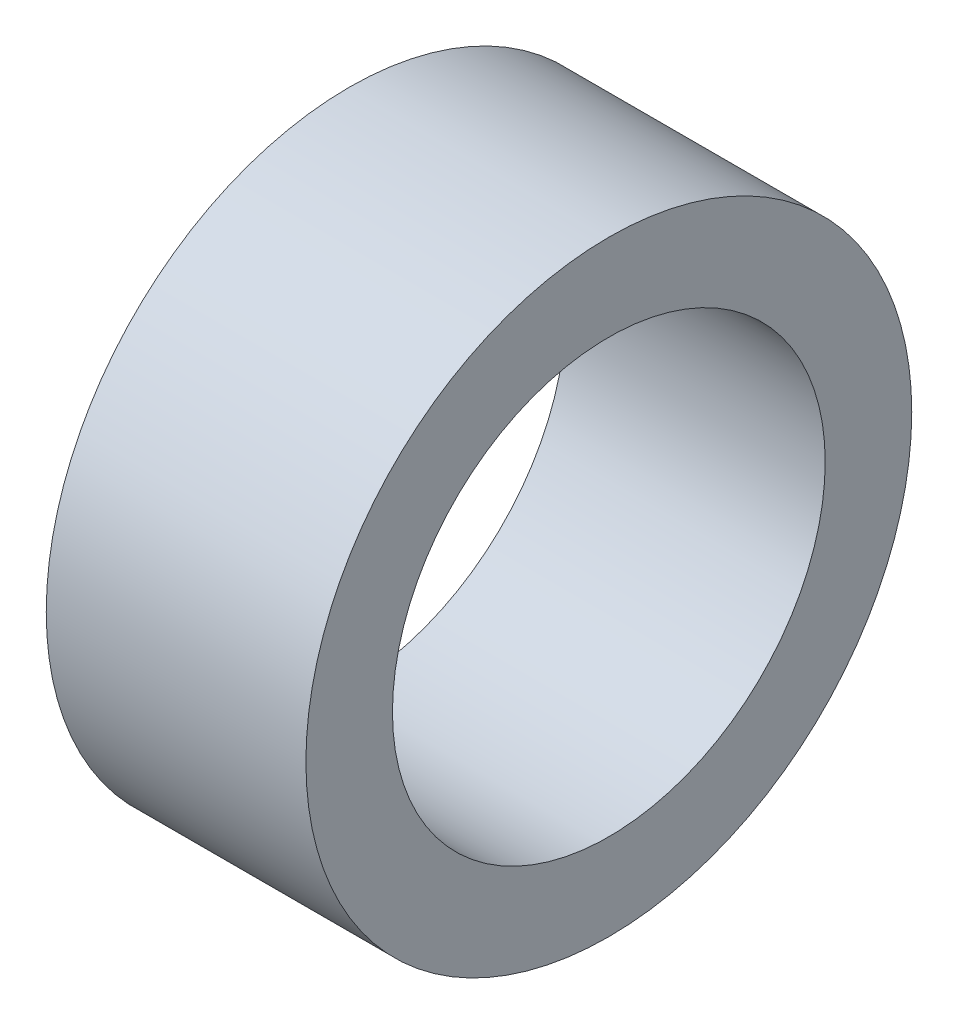
SolidWorks part; units mm, degrees
ref_plane "前视基准面" through (0, 0, 0) normal (0, 0, 1) x (1, 0, 0)
ref_plane "上视基准面" through (0, 0, 0) normal (0, 1, 0) x (1, 0, 0)
ref_plane "右视基准面" through (0, 0, 0) normal (1, 0, 0) x (0, 0, -1)
sketch "草图1" plane through (0, 0, 0) normal (1, 0, 0) x (0, 0, -1)
  circle A0 centre (0, 0) radius 7
  circle A1 centre (0, 0) radius 5
  dimension "D1" = 10
  dimension "D2" = 14
extrude "凸台-拉伸1" add sketch "草图1" along normal blind 6
